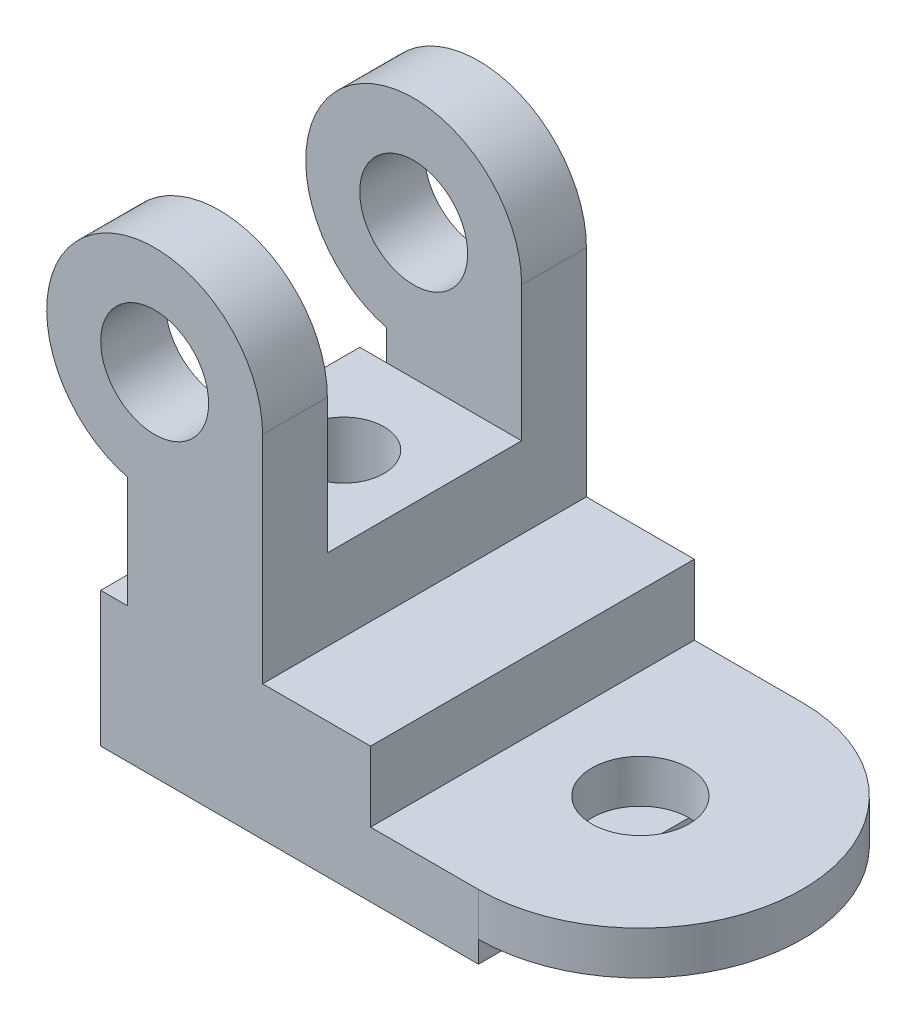
SolidWorks part; units mm, degrees
ref_plane "Front Plane" through (0, 0, 0) normal (0, 0, 1) x (1, 0, 0)
ref_plane "Top Plane" through (0, 0, 0) normal (0, 1, 0) x (1, 0, 0)
ref_plane "Right Plane" through (0, 0, 0) normal (1, 0, 0) x (0, 0, -1)
sketch "Sketch1" plane through (0, 0, 0) normal (0, 0, 1) x (1, 0, 0)
  line L0 (-35, 0) -> (35, 0)
  line L1 (35, 0) -> (35, 12)
  line L2 (-35, 0) -> (-35, 40)
  line L3 (35, 12) -> (15, 12)
  line L4 (15, 12) -> (15, 25)
  line L5 (15, 25) -> (-5, 25)
  line L6 (-35, 40) -> (-30, 40)
  line L7 (-5, 40) -> (-5, 25)
  line L8 (-5, 65) -> (-5, 40)
  line L9 (-30, 45.6351) -> (-30, 25)
  line L10 (-30, 25) -> (-35, 25)
  arc A0 (-5, 65) -> (-30, 45.6351) centre (-25, 65) ccw
  circle A1 centre (-25, 65) radius 10
  point P4 (0, 0)
  dimension "D9" = 65
  dimension "D12" = 20
  dimension "D1" = 70
  dimension "D2" = 12
  dimension "D3" = 40
  dimension "D4" = 20
  dimension "D5" = 13
  dimension "D6" = 20
  dimension "D7" = 60
  dimension "D8" = 25
  dimension "D10" = 25
  dimension "D11" = 15
extrude "Boss-Extrude1" add sketch "Sketch1" along normal mid plane 60 contours L8 A0 L9 L10 L2 L0 L1 L3 L4 L5 L7 A1
sketch "Sketch3" plane through (0, 12, 0) normal (0, 1, 0) x (1, 0, 0)
  line L0 (35, -30) -> (35, 30) construction
  line L1 (15, 30) -> (35, 30)
  line L2 (15, 30) -> (15, -30)
  line L3 (15, -30) -> (35, -30)
  arc A0 (35, -30) -> (35, 30) centre (35, 0) ccw
  dimension "D1" = 60
extrude "Boss-Extrude3" add sketch "Sketch3" against normal blind 8
sketch "Sketch4" plane through (0, 12, 0) normal (0, 1, 0) x (1, 0, 0)
  circle A0 centre (35, 0) radius 9
  dimension "D1" = 18
extrude "Cut-Extrude5" cut sketch "Sketch4" against normal blind 8
sketch "Sketch7" plane through (-5, 0, 0) normal (1, 0, 0) x (0, 0, -1)
  line L0 (0, 104.7785) -> (0, 10) construction
  line L2 (-18, 104.7785) -> (18, 104.7785)
  line L3 (-18, 104.7785) -> (-18, 40)
  line L4 (18, 104.7785) -> (18, 40)
  line L6 (-18, 40) -> (18, 40)
  line L7 (18, 104.7785) -> (18, -24.7196) construction
  line L8 (0, 104.7785) -> (0, -24.7196) construction
  line L9 (-18, 104.7785) -> (-18, -24.7196) construction
  dimension "D1" = 18
  dimension "D2" = 18
extrude "Cut-Extrude6" cut sketch "Sketch7" against normal through all
sketch "Sketch8" plane through (0, 40, 0) normal (0, 1, 0) x (1, 0, 0)
  line L1 (-5, 18) -> (-35, 18)
  line L2 (-5, 18) -> (-5, -18)
  line L3 (-5, -18) -> (-35, -18)
  line L4 (-35, 18) -> (-35, -18)
  dimension "D1" = 30
  dimension "D2" = 36
extrude "Boss-Extrude5" add sketch "Sketch8" against normal blind 15
sketch "Sketch9" plane through (0, 40, 0) normal (0, 1, 0) x (1, 0, 0)
  line L1 (-64.7742, 0) -> (73.9084, 0) construction
  line L3 (35, 45.2506) -> (35, -40.8184) construction
  line L4 (-35, 18) -> (-35, -18) construction
  line L5 (-45, -30) -> (-5, -30) construction
  circle A0 centre (-20, 0) radius 7.5
  dimension "D3" = 15
  dimension "D1" = 70
  dimension "D2" = 55
  dimension "D4" = 30
extrude "Cut-Extrude8" cut sketch "Sketch9" against normal through all
